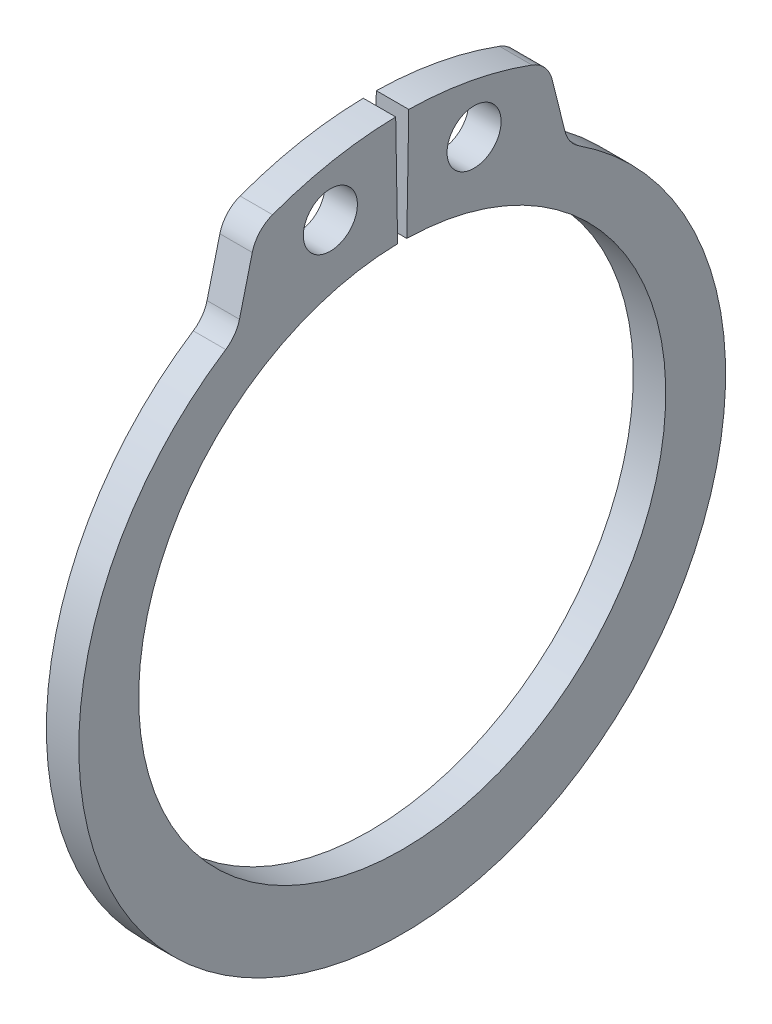
SolidWorks part; units mm, degrees
material "AISI 1085 Steel (Piano Wire)"
ref_plane "Front Plane" through (0, 0, 0) normal (0, 0, 1) x (1, 0, 0)
ref_plane "Top Plane" through (0, 0, 0) normal (0, 1, 0) x (1, 0, 0)
ref_plane "Right Plane" through (0, 0, 0) normal (1, 0, 0) x (0, 0, -1)
ref_plane "Plane1" through (-0.6, 0, 0) normal (-1, 0, 0) x (0, -1, 0)
sketch "Sketch1" plane through (-0.6, 0, 0) normal (-1, 0, 0) x (0, -1, 0)
  line L0 (-10.2545, 6.0207) -> (-12.1571, 5.5463)
  line L1 (-13.8479, 0.2417) -> (-9.7485, 0.1702)
  line L2 (-9.7485, -0.1702) -> (-13.8479, -0.2417)
  line L3 (-12.1571, -5.5463) -> (-10.2545, -6.0207)
  circle A0 centre (-11.7554, -2.6581) radius 1
  circle A1 centre (-11.7554, 2.6581) radius 1
  arc A2 (-12.1571, 5.5463) -> (-12.9925, 4.7976) centre (-11.8668, 4.3819) ccw
  arc A3 (-12.9925, 4.7976) -> (-13.8479, 0.2417) centre (0, 0) ccw
  arc A4 (-9.7485, 0.1702) -> (-9.7485, -0.1702) centre (0, 0) cw
  arc A5 (-13.8479, -0.2417) -> (-12.9925, -4.7976) centre (0, 0) ccw
  arc A6 (-12.9925, -4.7976) -> (-12.1571, -5.5463) centre (-11.8668, -4.3819) ccw
  arc A7 (-10.2545, -6.0207) -> (-9.5393, -6.5301) centre (-10.5448, -7.185) cw
  arc A8 (-9.5393, -6.5301) -> (-9.5393, 6.5301) centre (0.4857, 0) ccw
  arc A9 (-9.5393, 6.5301) -> (-10.2545, 6.0207) centre (-10.5448, 7.185) cw
extrude "Boss-Extrude1" add sketch "Sketch1" against normal blind 1.2
